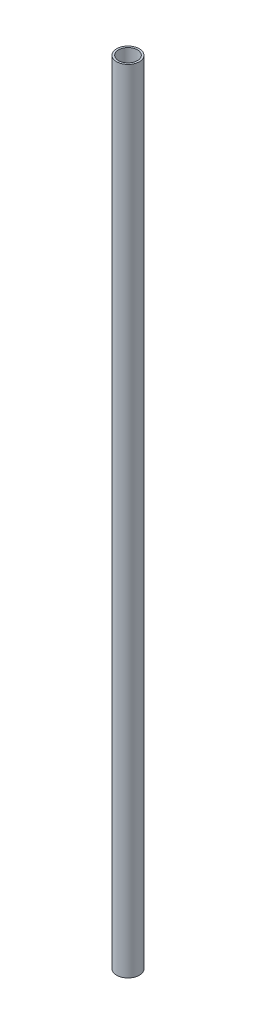
SolidWorks part; units mm, degrees
material "Amazon CF"
ref_plane "Front Plane" through (0, 0, 0) normal (0, 0, 1) x (1, 0, 0)
ref_plane "Top Plane" through (0, 0, 0) normal (0, 1, 0) x (1, 0, 0)
ref_plane "Right Plane" through (0, 0, 0) normal (1, 0, 0) x (0, 0, -1)
sketch "Sketch3" plane through (0, 0, -4.9372) normal (0, 1, 0) x (1, 0, 0)
  line L0 (-55, -4.9372) -> (55, -4.9372) construction
  line L1 (0, -59.9372) -> (0, 50.0628) construction
  circle A1 centre (0, -4.9372) radius 6
  circle A4 centre (0, -4.9372) radius 5
  point P1 (-4.2806, -2.9168)
  point P6 (0, 0)
  dimension "D1" = 10
  dimension "D2" = 12
extrude "Boss-Extrude2" add sketch "Sketch3" along normal blind 420
